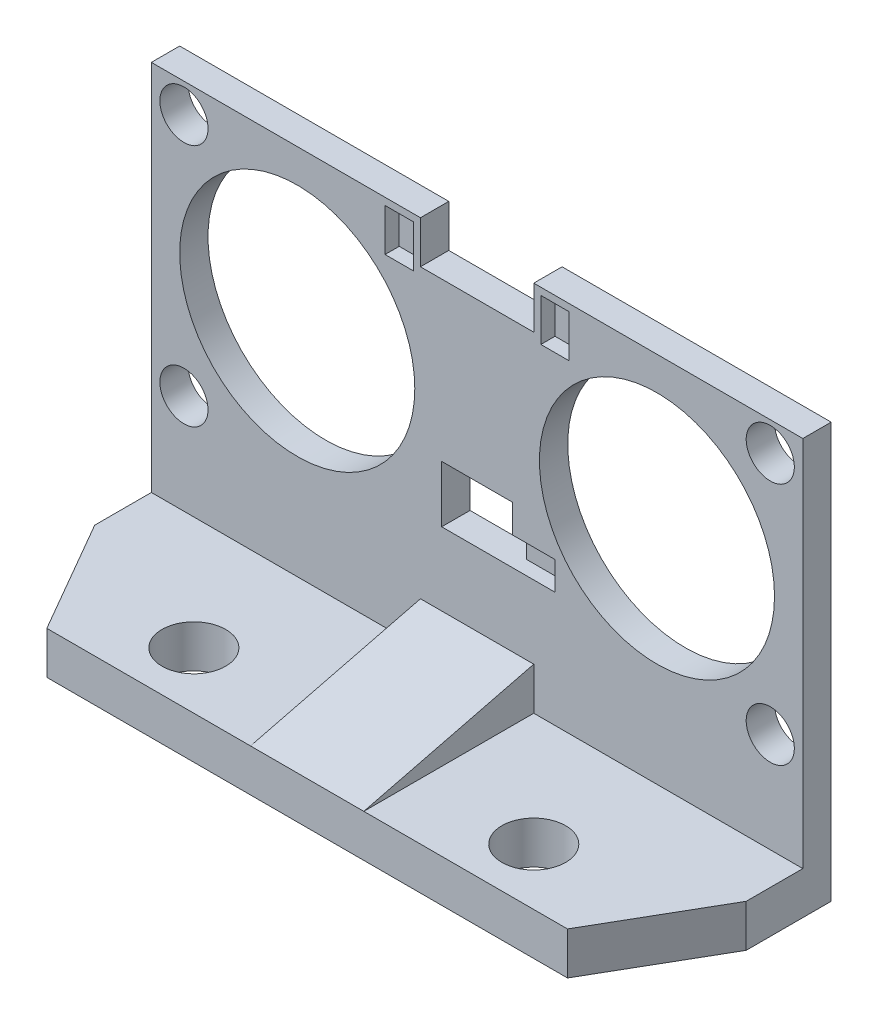
SolidWorks part; units mm, degrees
material "ABS"
ref_plane "前基準面" through (0, 0, 0) normal (0, 0, 1) x (1, 0, 0)
ref_plane "上基準面" through (0, 0, 0) normal (0, 1, 0) x (1, 0, 0)
ref_plane "右基準面" through (0, 0, 0) normal (1, 0, 0) x (0, 0, -1)
sketch "草圖1" plane through (0, 0, 0) normal (0, 0, 1) x (1, 0, 0)
  line L1 (-23, -10.65) -> (23, -10.65)
  line L2 (-23, -10.65) -> (-23, 10.65)
  line L3 (-23, 10.65) -> (23, 10.65)
  line L4 (23, -10.65) -> (23, 10.65)
  line L5 (-23, -10.65) -> (23, 10.65) construction
  line L6 (-23, 10.65) -> (23, -10.65) construction
  point P0 (0, 0)
  dimension "D1" = 46
  dimension "D2" = 21.3
extrude "填料-伸長1" add sketch "草圖1" along normal blind 2
sketch "草圖2" plane through (0, 0, 2) normal (0, 0, 1) x (1, 0, 0)
  line L0 (-12.7, 0) -> (12.7, 0) construction
  circle A0 centre (-12.7, 0) radius 8.3
  circle A1 centre (12.7, 0) radius 8.3
  point P4 (0, 0)
  dimension "D1" = 25.4
  dimension "D2" = 16.6
extrude "除料-伸長1" cut sketch "草圖2" against normal through all
sketch "草圖3" plane through (0, 0, 2) normal (0, 0, 1) x (1, 0, 0)
  line L0 (0, 0) -> (0, 9.15) construction
  line L1 (23, 10.65) -> (-23, 10.65) construction
  line L2 (-4, 7.65) -> (4, 7.65)
  line L3 (-4, 7.65) -> (-4, 10.65)
  line L4 (-4, 10.65) -> (4, 10.65)
  line L5 (4, 7.65) -> (4, 10.65)
  line L6 (-4, 7.65) -> (4, 10.65) construction
  line L7 (-4, 10.65) -> (4, 7.65) construction
  dimension "D1" = 8
  dimension "D2" = 3
extrude "除料-伸長2" cut sketch "草圖3" against normal through all
sketch "草圖4" plane through (0, 0, 2) normal (0, 0, 1) x (1, 0, 0)
  line L0 (0, 0) -> (0, -5.5) construction
  line L2 (-2.5, -3.5) -> (2.5, -3.5)
  line L3 (-2.5, -3.5) -> (-2.5, -7.5)
  line L4 (-2.5, -7.5) -> (2.5, -7.5)
  line L5 (2.5, -3.5) -> (2.5, -7.5)
  line L6 (-2.5, -3.5) -> (2.5, -7.5) construction
  line L7 (-2.5, -7.5) -> (2.5, -3.5) construction
  dimension "D1" = 5
  dimension "D2" = 4
  dimension "D3" = 5.5
extrude "除料-伸長3" cut sketch "草圖4" against normal through all
sketch "草圖5" plane through (0, 0, 2) normal (0, 0, 1) x (1, 0, 0)
  line L0 (0, 0) -> (0, 8.65) construction
  line L1 (2.5, -7.5) -> (5.5, -7.5)
  line L2 (2.5, -7.5) -> (2.5, -5.5)
  line L3 (2.5, -5.5) -> (5.5, -5.5)
  line L4 (5.5, -7.5) -> (5.5, -5.5)
  line L5 (-5.5, 8.65) -> (5.5, 8.65) construction
  line L6 (23, 10.65) -> (4, 10.65) construction
  line L7 (-4.5, 10.15) -> (-6.5, 10.15)
  line L8 (-4.5, 10.15) -> (-4.5, 7.15)
  line L9 (-4.5, 7.15) -> (-6.5, 7.15)
  line L10 (-6.5, 10.15) -> (-6.5, 7.15)
  line L11 (-4.5, 10.15) -> (-6.5, 7.15) construction
  line L12 (-4.5, 7.15) -> (-6.5, 10.15) construction
  line L13 (6.5, 10.15) -> (4.5, 10.15)
  line L14 (6.5, 10.15) -> (6.5, 7.15)
  line L15 (6.5, 7.15) -> (4.5, 7.15)
  line L16 (4.5, 10.15) -> (4.5, 7.15)
  line L17 (6.5, 10.15) -> (4.5, 7.15) construction
  line L18 (6.5, 7.15) -> (4.5, 10.15) construction
  point P10 (0, 8.65)
  dimension "D1" = 2
  dimension "D2" = 3
  dimension "D3" = 2
  dimension "D4" = 3
  dimension "D5" = 11
  dimension "D6" = 0.5
extrude "除料-伸長4" cut sketch "草圖5" against normal blind 1
sketch "草圖8" plane through (0, -10.65, 0) normal (0, -1, 0) x (1, 0, 0)
  line L1 (-23, 2) -> (23, 2)
  line L2 (-23, 2) -> (-23, 0)
  line L3 (-23, 0) -> (23, 0)
  line L4 (23, 2) -> (23, 0)
extrude "填料-伸長2" add sketch "草圖8" along normal blind 5
sketch "草圖9" plane through (0, -15.65, 0) normal (0, -1, 0) x (1, 0, 0)
  line L1 (-23, 0) -> (23, 0)
  line L2 (-23, 0) -> (-23, 14)
  line L3 (-23, 14) -> (23, 14)
  line L4 (23, 0) -> (23, 14)
  dimension "D1" = 14
extrude "填料-伸長3" add sketch "草圖9" along normal blind 3
hole_wizard "M3 餘隙孔1" positions "草圖6" profile "草圖7" hole size "M3" standard "Ansi Metric" end condition through all
sketch "草圖6" plane through (0, 0, 2) normal (0, 0, 1) x (1, 0, 0)
  line L1 (-20.7, -8.6) -> (20.7, -8.6) construction
  line L2 (-20.7, -8.6) -> (-20.7, 8.6) construction
  line L3 (-20.7, 8.6) -> (20.7, 8.6) construction
  line L4 (20.7, -8.6) -> (20.7, 8.6) construction
  line L5 (-20.7, -8.6) -> (20.7, 8.6) construction
  line L6 (-20.7, 8.6) -> (20.7, -8.6) construction
  point P1 (20.7, 8.6)
  point P112 (-20.7, -8.6)
  point P113 (-20.7, 8.6)
  point P114 (20.7, -8.6)
  dimension "D1" = 17.2
  dimension "D2" = 41.4
sketch "草圖7" plane through (20.7, 8.6, 2) normal (1, 0, 0) x (0, -1, 0)
  line L0 (0, 0) -> (0, 2)
  line L1 (0, 2) -> (1.7, 2)
  line L2 (1.7, 2) -> (1.7, 0)
  line L5 (1.7, 0) -> (0, 0)
  line L11 (0, -6.35) -> (0, 107.95) construction
  dimension "貫穿孔直徑" = 3.4
  dimension "貫穿孔深度" = 2
hole_wizard "M4 餘隙孔1" positions "草圖10" profile "草圖11" hole size "M4" standard "Ansi Metric" end condition through all
sketch "草圖10" plane through (0, -15.65, 0) normal (0, 1, 0) x (1, 0, 0)
  line L0 (0, -14) -> (0, -10) construction
  line L1 (23, -14) -> (-23, -14) construction
  line L4 (-12, -10) -> (12, -10) construction
  point P8 (-12, -10)
  point P9 (12, -10)
  dimension "D1" = 24
  dimension "D2" = 4
sketch "草圖11" plane through (12, -15.65, 10) normal (1, 0, 0) x (0, 0, 1)
  line L0 (0, 0) -> (0, 3)
  line L1 (0, 3) -> (2.25, 3)
  line L2 (2.25, 3) -> (2.25, 0)
  line L5 (2.25, 0) -> (0, 0)
  line L11 (0, -6.35) -> (0, 107.95) construction
  dimension "貫穿孔直徑" = 4.5
  dimension "貫穿孔深度" = 3
sketch "草圖13" plane through (0, 0, 0) normal (1, 0, 0) x (0, 0, -1)
  line L0 (-2, -12.65) -> (-14, -15.65)
  line L1 (-2, -15.65) -> (-2, 10.65) construction
  line L2 (-2, -15.65) -> (-14, -15.65) construction
  dimension "D1" = 3
rib "肋材1" sketch "草圖13" sketch "草圖13" thickness 8 extrusion direction parallel to sketch draft on no parameters "D1"=8
chamfer "導角1" distance 8 angle 30 2 edges at (-23, -17.15, 14) (23, -17.15, 14)
